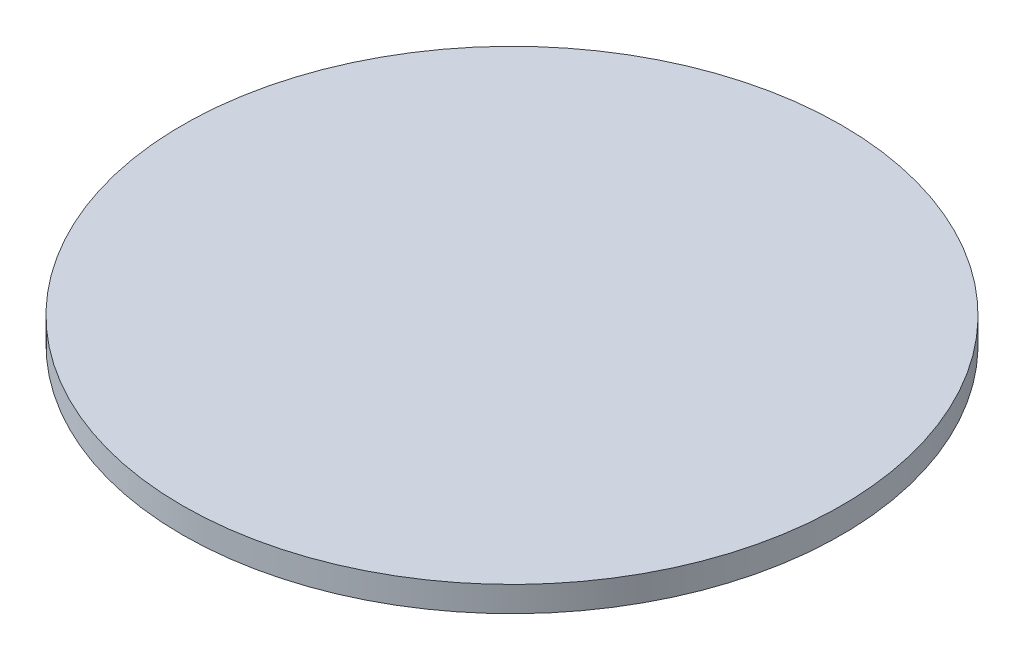
SolidWorks part; units mm, degrees
ref_plane "Front Plane" through (0, 0, 0) normal (0, 0, 1) x (1, 0, 0)
ref_plane "Top Plane" through (0, 0, 0) normal (0, 1, 0) x (1, 0, 0)
ref_plane "Right Plane" through (0, 0, 0) normal (1, 0, 0) x (0, 0, -1)
sketch "Sketch1" plane through (0, 0, 0) normal (0, 1, 0) x (1, 0, 0)
  circle A0 centre (0, 0) radius 82.55
  dimension "D1" = 165.1
extrude "Boss-Extrude1" add sketch "Sketch1" along normal blind 6.35
